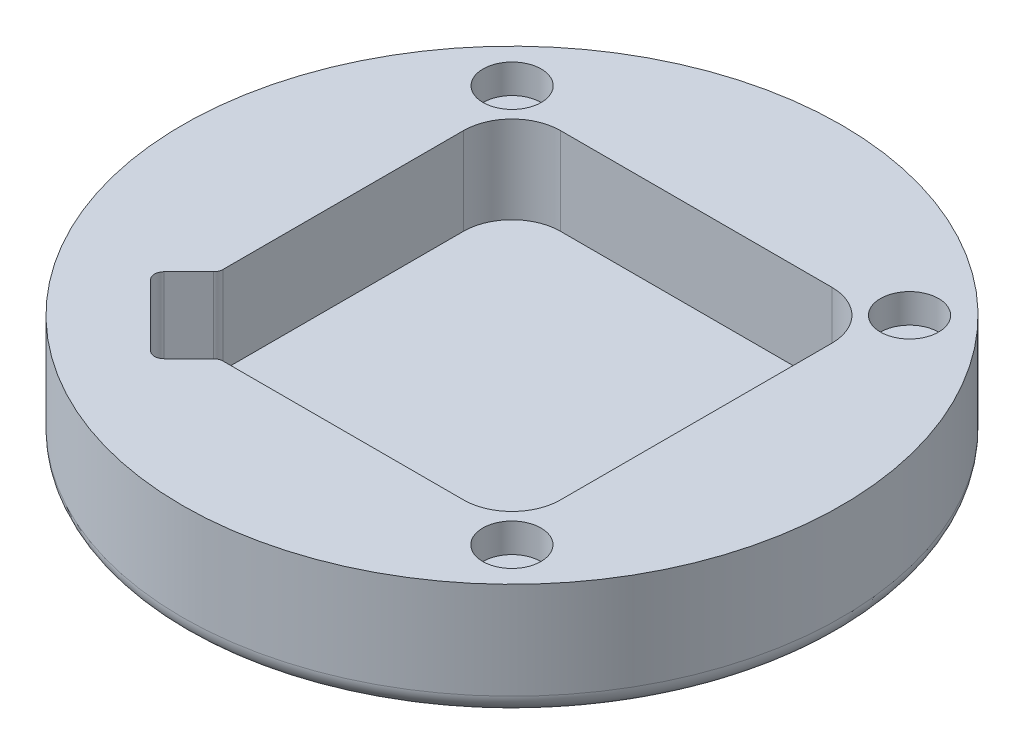
SolidWorks part; units mm, degrees
ref_plane "Front Plane" through (0, 0, 0) normal (0, 0, 1) x (1, 0, 0)
ref_plane "Top Plane" through (0, 0, 0) normal (0, 1, 0) x (1, 0, 0)
ref_plane "Right Plane" through (0, 0, 0) normal (1, 0, 0) x (0, 0, -1)
sketch "Sketch1" plane through (0, 0, 0) normal (0, 1, 0) x (1, 0, 0)
  circle A0 centre (0, 0) radius 34
  dimension "D1" = 68
extrude "Boss-Extrude1" add sketch "Sketch1" along normal blind 3
sketch "Sketch2" plane through (0, 3, 0) normal (0, 1, 0) x (1, 0, 0)
  line L1 (-19, -19) -> (19, -19)
  line L2 (-19, -19) -> (-19, 19)
  line L3 (-19, 19) -> (19, 19)
  line L4 (19, -19) -> (19, 19)
  line L5 (-19, -19) -> (19, 19) construction
  line L6 (-19, 19) -> (19, -19) construction
  circle A1 centre (0, 0) radius 34
  dimension "D1" = 38
  dimension "D2" = 38
extrude "Boss-Extrude2" add sketch "Sketch2" along normal blind 9
fillet "Fillet1" radius 5 4 edges at (19, 7.5, 19) (-19, 7.5, 19) (19, 7.5, -19) (-19, 7.5, -19)
sketch "Sketch3" plane through (0, 12, 0) normal (0, 1, 0) x (1, 0, 0)
  line L0 (-19, 14) -> (-19, -14) construction
  line L1 (14, 19) -> (-14, 19) construction
  circle A0 centre (-20.5, 20.5122) radius 3
  circle A1 centre (0, 0) radius 29 construction
  circle A2 centre (20.5122, 20.5) radius 3
  circle A3 centre (20.5, -20.5122) radius 3
  circle A4 centre (-20.5122, -20.5) radius 3 [skipped]
  point P18 (0, 0)
  dimension "D1" = 6
  dimension "D2" = 58
  dimension "D3" = 1.5
  dimension "D4" = 1.5122
  dimension "D5" = 4
extrude "Cut-Extrude1" cut sketch "Sketch3" against normal blind 3
sketch "Sketch4" plane through (0, 12, 0) normal (0, 1, 0) x (1, 0, 0)
  line L0 (-19, -11.2218) -> (-22.5355, -14.7574)
  line L1 (-19, 14) -> (-19, -14) construction
  line L2 (-22.5355, -14.7574) -> (-17.1394, -20.1535)
  line L3 (-17.1394, -20.1535) -> (-14.7574, -22.5355)
  line L4 (-14.7574, -22.5355) -> (-11.2218, -19)
  line L5 (-14, -19) -> (14, -19) construction
  line L6 (-11.2218, -19) -> (-19, -11.2218)
  line L7 (-17.5355, -17.5355) -> (-24.0416, -24.0416) construction
  arc A0 (-19, -14) -> (-14, -19) centre (-14, -14) ccw construction
  circle A1 centre (0, 0) radius 34 construction
  dimension "D1" = 135
  dimension "D2" = 5
  dimension "D3" = 11
extrude "Cut-Extrude2" cut sketch "Sketch4" against normal blind 9
fillet "Fillet2" radius 1 4 edges at (-19, 7.5, 11.2218) (-11.2218, 7.5, 19) (-14.7574, 7.5, 22.5355) (-22.5355, 7.5, 14.7574)
fillet "Fillet3" radius 2 1 edges at (0, 0, 34)
